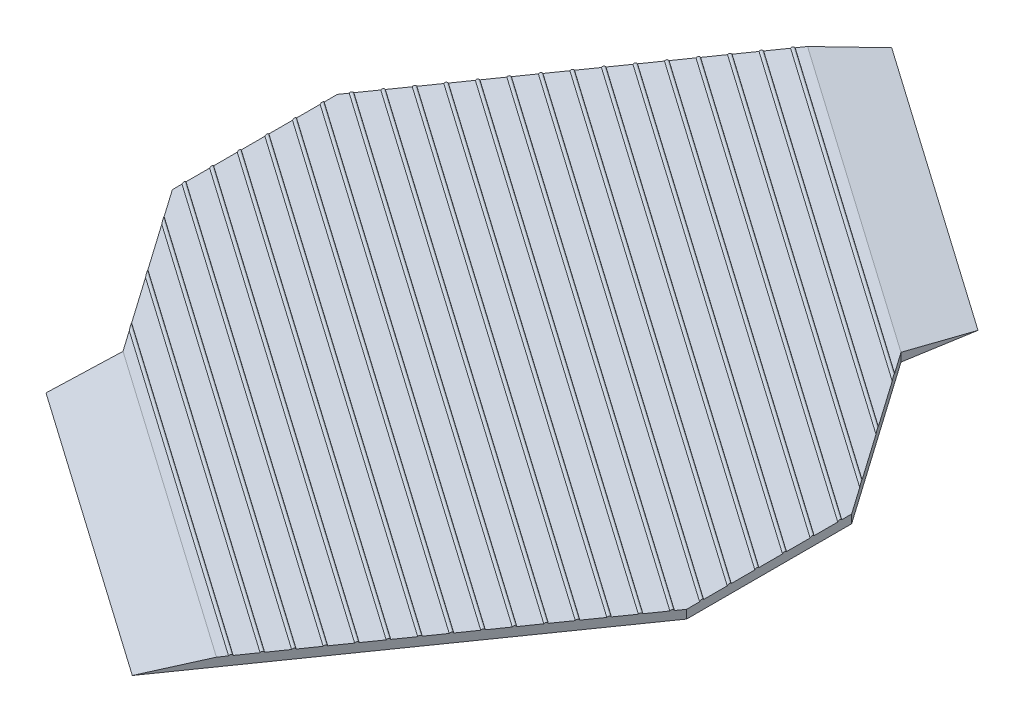
SolidWorks part; units mm, degrees
ref_plane "前视基准面" through (0, 0, 0) normal (0, 0, 1) x (1, 0, 0)
ref_plane "上视基准面" through (0, 0, 0) normal (0, 1, 0) x (1, 0, 0)
ref_plane "右视基准面" through (0, 0, 0) normal (1, 0, 0) x (0, 0, -1)
other "Configuration Table"
sketch "草图2" plane through (0, 0, 0) normal (0, 1, 0) x (1, 0, 0)
  line L0 (-2614.5278, 2403) -> (1483.4722, 2403)
  line L1 (1483.4722, 2403) -> (2154.0992, 1933.4219)
  line L2 (2154.0992, 1933.4219) -> (3290, 311.1874)
  line L3 (3290, 311.1874) -> (3290, -1438.3258)
  line L4 (3290, -1438.3258) -> (2614.5278, -2403)
  line L5 (2614.5278, -2403) -> (-1483.4722, -2403)
  line L8 (-3290, -311.1874) -> (-3290, 1438.3258)
  line L9 (-3290, 1438.3258) -> (-2614.5278, 2403)
  line L10 (-3290, -311.1874) -> (-2154.0992, -1933.4219)
  line L11 (-2154.0992, -1933.4219) -> (-1483.4722, -2403)
  line L12 (1483.4722, 2403) -> (3290, 2403) construction
  line L13 (3290, 2403) -> (3290, 311.1874) construction
  line L14 (3290, -1438.3258) -> (3290, -2403) construction
  line L15 (3290, -2403) -> (2614.5278, -2403) construction
  line L16 (-1483.4722, -2403) -> (-3290, -2403) construction
  line L17 (-3290, -2403) -> (-3290, -311.1874) construction
  line L18 (-2614.5278, 2403) -> (-3290, 2403) construction
  line L19 (-3290, 2403) -> (-3290, 1438.3258) construction
  line L20 (3290, 2403) -> (-3290, -2403) construction
  line L21 (3290, -2403) -> (0, 0) construction
  line L22 (0, 0) -> (-3290, 2403) construction
  dimension "D1" = 4098
  dimension "D2" = 4806
  dimension "D3" = 6580
  dimension "D4" = 55
  dimension "D5" = 3520
  dimension "D6" = 3520
  dimension "D7" = 55
  dimension "D8" = 2873.5
  dimension "D9" = 2873.5
  dimension "D10" = 4098
extrude "凸台-拉伸1" add sketch "草图2" along normal blind 90 contours L22 L20 L2 L1 L0 L9 | L20 L22 L9 L8 L10 L11 | L4 L21 L20 L11 L5 | L21 L4 L3 L2 L20
sketch "草图5" plane through (0, 90, 0) normal (0, 1, 0) x (1, 0, 0)
  line L0 (2614.5278, -2403) -> (320.2221, -5679.6082)
  line L1 (869.3656, -4895.35) -> (-2183.4777, -2757.7261)
  line L2 (1236.4545, -4371.0927) -> (-2066.7576, -2058.1587)
  line L3 (-2154.0992, -1933.4219) -> (-2066.7576, -2058.1587)
  line L4 (-2183.4777, -2757.7261) -> (-2066.7576, -2058.1587)
  line L10 (-3290, -311.1874) -> (-2154.0992, -1933.4219)
  line L11 (-2154.0992, -1933.4219) -> (-1483.4722, -2403)
  line L12 (-1483.4722, -2403) -> (2614.5278, -2403)
  line L13 (2614.5278, -2403) -> (3290, -1438.3258)
  line L14 (3290, -1438.3258) -> (3290, 311.1874)
  line L15 (3290, 311.1874) -> (2154.0992, 1933.4219)
  line L16 (2154.0992, 1933.4219) -> (1483.4722, 2403)
  line L17 (1483.4722, 2403) -> (-2614.5278, 2403)
  line L18 (-2614.5278, 2403) -> (-3290, 1438.3258)
  line L19 (-3290, 1438.3258) -> (-3290, -311.1874)
  line L20 (-3290, -311.1874) -> (-2154.0992, -1933.4219)
  line L21 (-2154.0992, -1933.4219) -> (-1483.4722, -2403)
  line L22 (-1483.4722, -2403) -> (2614.5278, -2403)
  line L23 (2614.5278, -2403) -> (3290, -1438.3258)
  line L24 (3290, -1438.3258) -> (3290, 311.1874)
  line L25 (3290, 311.1874) -> (2154.0992, 1933.4219)
  line L26 (2154.0992, 1933.4219) -> (1483.4722, 2403)
  line L27 (1483.4722, 2403) -> (-2614.5278, 2403)
  line L28 (-2614.5278, 2403) -> (-3290, 1438.3258)
  line L29 (-3290, 1438.3258) -> (-3290, -311.1874)
  line M13 (-2154.0992, -1933.4219) -> (-1483.4722, -2403)
  line M14 (-1483.4722, -2403) -> (2614.5278, -2403)
  dimension "D2" = 4000
  dimension "D3" = 3726.8335
  dimension "D4" = 692.0813
  dimension "D5" = 640
  dimension "D1" = 0
extrude "凸台-拉伸2" add sketch "草图5" against normal blind 90 separate body contours L3 L2 L0 M13 M14 | L4 L1 L0 L2
sketch "草图6" plane through (2883.4152, 0, 2018.9891) normal (0.8192, 0, 0.5736) x (0.5736, 0, -0.8192)
  line L0 (-3511.3883, 0) -> (-2871.005, 90)
  line L1 (708.859, 90) -> (-468.7908, 90) construction
  line L2 (708.859, 0) -> (-468.7908, 0) construction
  line L5 (-2871.005, 90) -> (-3511.3883, 90)
  line L6 (-3511.3883, 90) -> (-3511.3883, 0)
  line L7 (-3511.3883, 0) -> (-3511.3883, 90) construction
  line L8 (-468.7908, 0) -> (-3511.3883, 0) construction
  dimension "D1" = 8
extrude "切除-拉伸1" cut sketch "草图6" against normal through all
pattern_circular "阵列(圆周)2" count 2 over 360 about axis through (0, 0, 0) along (0, 1, 0) of bodies 108
sketch "草图9" plane through (2883.4152, 0, 2018.9891) normal (0.8192, 0, 0.5736) x (0.5736, 0, -0.8192)
  line L2 (-2761.005, 80.3) -> (-2761.005, 100.3) construction
  line L3 (-468.7908, 90) -> (-2871.005, 90) construction
  circle A0 centre (-2761.005, 80.3) radius 20
  dimension "D1" = 40
  dimension "D2" = 10.3
  dimension "D3" = 110
extrude "凸台-拉伸3" add sketch "草图9" against normal blind 8000
pattern_linear "阵列(线性)1" count 24 spacing 240 along (0.5736, 0, -0.8192) of "凸台-拉伸3"
sketch "草图10" plane through (0, 0, 0) normal (0, -1, 0) x (1, 0, 0)
  line L11 (-7000, 7000) -> (7000, 7000)
  line L12 (-7000, 7000) -> (-7000, -7000)
  line L13 (-7000, -7000) -> (7000, -7000)
  line L14 (7000, 7000) -> (7000, -7000)
  line L15 (0, -7000) -> (0, 7000) construction
  line L16 (-7000, 0) -> (7000, 0) construction
  line L20 (2066.7576, -2058.1587) -> (3290, -311.1874)
  line L21 (3290, -311.1874) -> (3290, 1438.3258)
  line L22 (3290, 1438.3258) -> (869.3656, 4895.35)
  line L23 (869.3656, 4895.35) -> (-2183.4777, 2757.7261)
  line L24 (-2183.4777, 2757.7261) -> (-2066.7576, 2058.1587)
  line L25 (-2066.7576, 2058.1587) -> (-3290, 311.1874)
  line L26 (-3290, 311.1874) -> (-3290, -1438.3258)
  line L27 (-3290, -1438.3258) -> (-869.3656, -4895.35)
  line L28 (-869.3656, -4895.35) -> (2183.4777, -2757.7261)
  line L29 (2183.4777, -2757.7261) -> (2066.7576, -2058.1587)
  line L30 (2066.7576, -2058.1587) -> (3290, -311.1874)
  line L31 (3290, -311.1874) -> (3290, 1438.3258)
  line L32 (3290, 1438.3258) -> (869.3656, 4895.35)
  line L33 (869.3656, 4895.35) -> (-2183.4777, 2757.7261)
  line L34 (-2183.4777, 2757.7261) -> (-2066.7576, 2058.1587)
  line L35 (-2066.7576, 2058.1587) -> (-3290, 311.1874)
  line L36 (-3290, 311.1874) -> (-3290, -1438.3258)
  line L37 (-3290, -1438.3258) -> (-869.3656, -4895.35)
  line L38 (-869.3656, -4895.35) -> (2183.4777, -2757.7261)
  line L39 (2183.4777, -2757.7261) -> (2066.7576, -2058.1587)
  point P0 (0, 0)
  dimension "D2" = 14000
  dimension "D3" = 14000
  dimension "D1" = 0
extrude "切除-拉伸2" cut sketch "草图10" against normal blind 8000
ref_plane "基准面1" through (0, 0, 0) normal (0.7071, 0, -0.7071) x (-0.7071, 0, -0.7071)
ref_plane "基准面2" through (0, 0, 0) normal (0.7071, 0, 0.7071) x (0.7071, 0, -0.7071)
